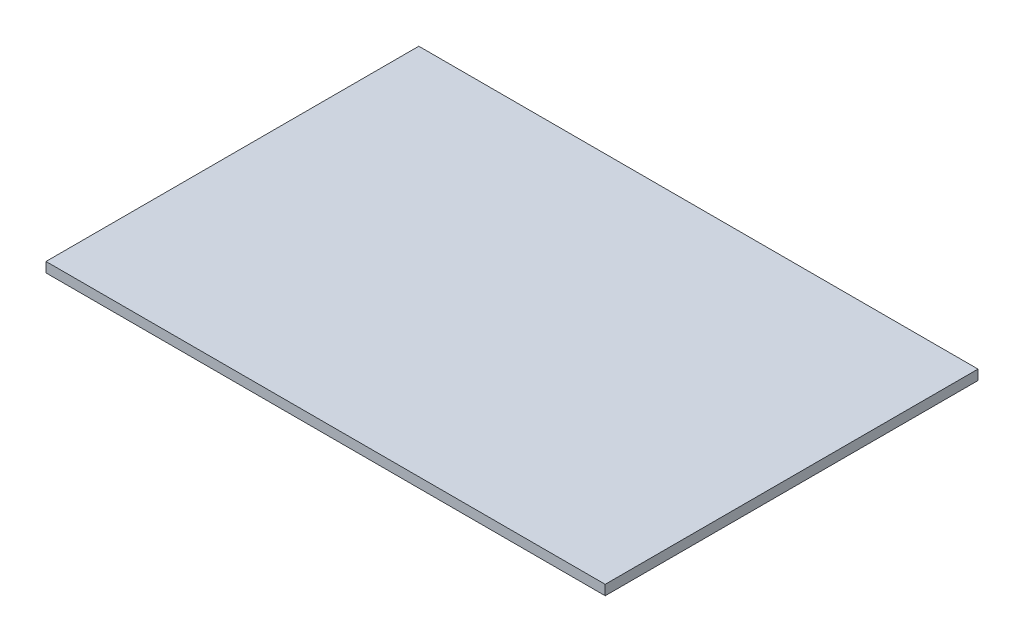
SolidWorks part; units mm, degrees
ref_plane "Front Plane" through (0, 0, 0) normal (0, 0, 1) x (1, 0, 0)
ref_plane "Top Plane" through (0, 0, 0) normal (0, 1, 0) x (1, 0, 0)
ref_plane "Right Plane" through (0, 0, 0) normal (1, 0, 0) x (0, 0, -1)
sketch "Sketch1" plane through (0, 0, 0) normal (0, 1, 0) x (1, 0, 0)
  line L0 (-450, -300) -> (-450, 300)
  line L1 (-450, -300) -> (450, -300)
  line L3 (-450, 300) -> (450, 300)
  line L4 (450, -300) -> (450, 300)
  dimension "D1" = 900
  dimension "D2" = 600
  dimension "D3" = 450
  dimension "D4" = 300
extrude "Boss-Extrude1" add sketch "Sketch1" along normal blind 16
